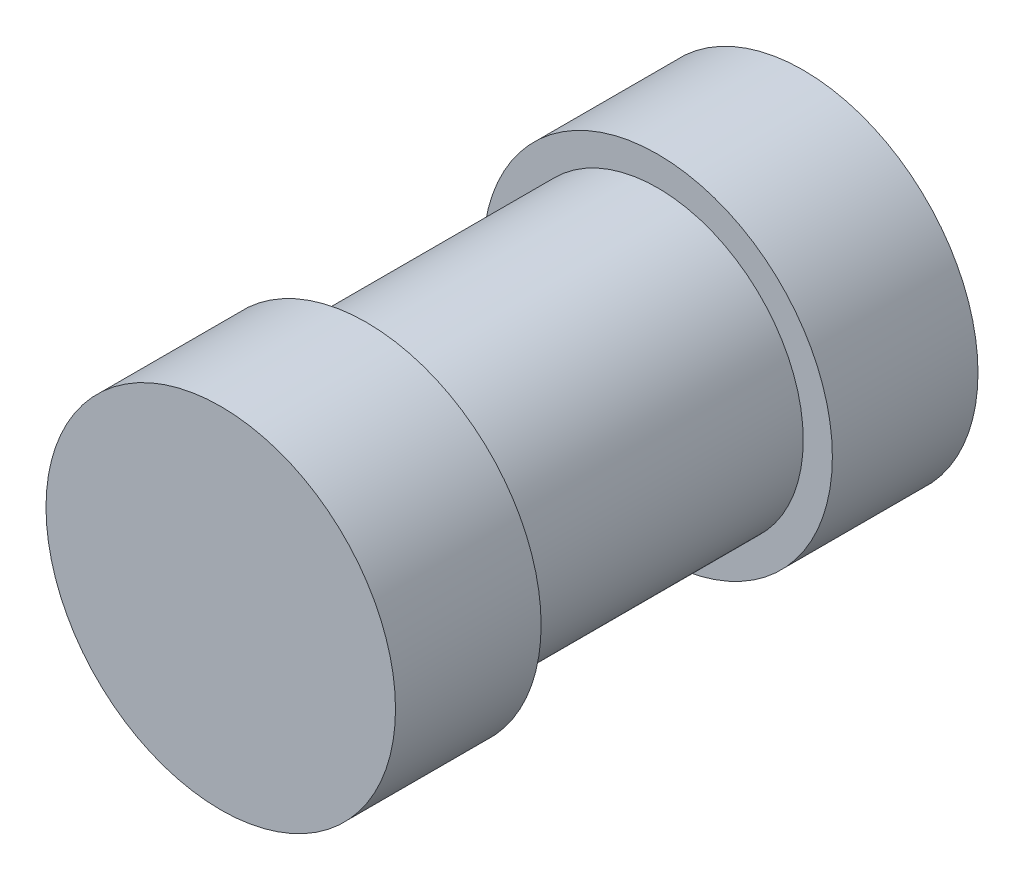
SolidWorks part; units mm, degrees
material "6061-T6 (SS)"
ref_plane "Front Plane" through (0, 0, 0) normal (0, 0, 1) x (1, 0, 0)
ref_plane "Top Plane" through (0, 0, 0) normal (0, 1, 0) x (1, 0, 0)
ref_plane "Right Plane" through (0, 0, 0) normal (1, 0, 0) x (0, 0, -1)
sketch "Sketch1" plane through (0, 0, 0) normal (0, 0, 1) x (1, 0, 0)
  circle A0 centre (0, 0) radius 3.175
  dimension "D1" = 6.35
extrude "Boss-Extrude1" add sketch "Sketch1" along normal blind 6.35
sketch "Sketch2" plane through (0, 0, 6.35) normal (0, 0, 1) x (1, 0, 0)
  circle A0 centre (0, 0) radius 3.81
  dimension "D1" = 7.62
extrude "Boss-Extrude2" add sketch "Sketch2" along normal blind 3.175
sketch "Sketch3" plane through (0, 0, 0) normal (0, 0, -1) x (-1, 0, 0)
  circle A0 centre (0, 0) radius 3.81
  dimension "D1" = 7.62
extrude "Boss-Extrude3" add sketch "Sketch3" along normal blind 3.175
